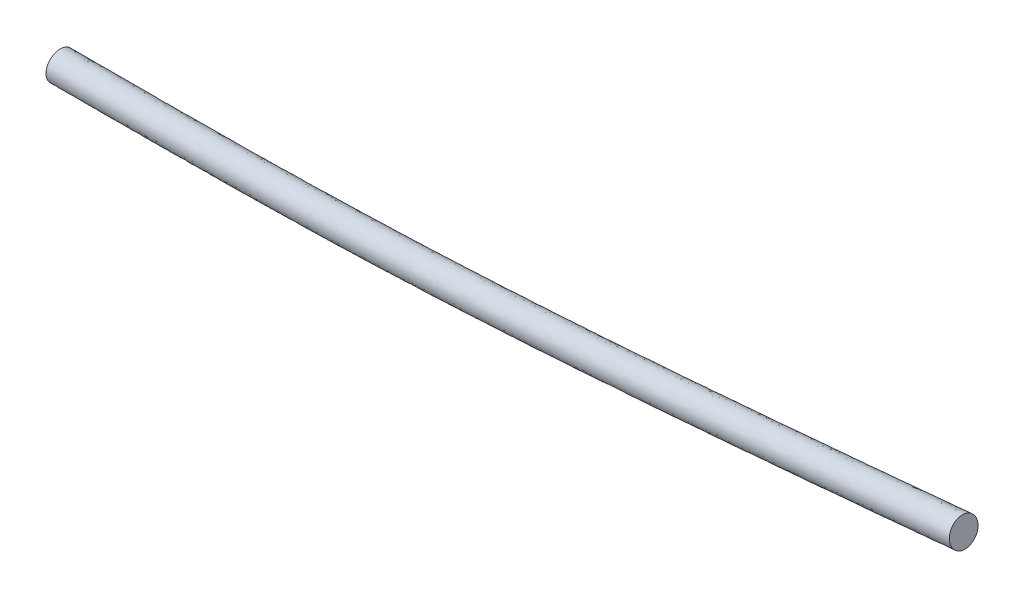
SolidWorks part; units mm, degrees
ref_plane "Front Plane" through (0, 0, 0) normal (0, 0, 1) x (1, 0, 0)
ref_plane "Top Plane" through (0, 0, 0) normal (0, 1, 0) x (1, 0, 0)
ref_plane "Right Plane" through (0, 0, 0) normal (1, 0, 0) x (0, 0, -1)
sketch "Sketch1" plane through (0, 0, 0) normal (0, 0, 1) x (1, 0, 0)
  spline S0 degree 3 poles (0, 0) (31.4447, 0) (45.5282, 0.3322) (94.9943, 5) knots 0 0 0 0 1 1 1 1
  dimension "D1" = 5
sketch "Sketch2" plane through (0, 0, 0) normal (1, 0, 0) x (0, 0, -1)
  line L0 (0, 5) -> (0, 0) construction
  circle A0 centre (0, 1.5) radius 1.5
  dimension "D1" = 3
sweep "Sweep1" add profiles "Sketch2" path "Sketch1"
